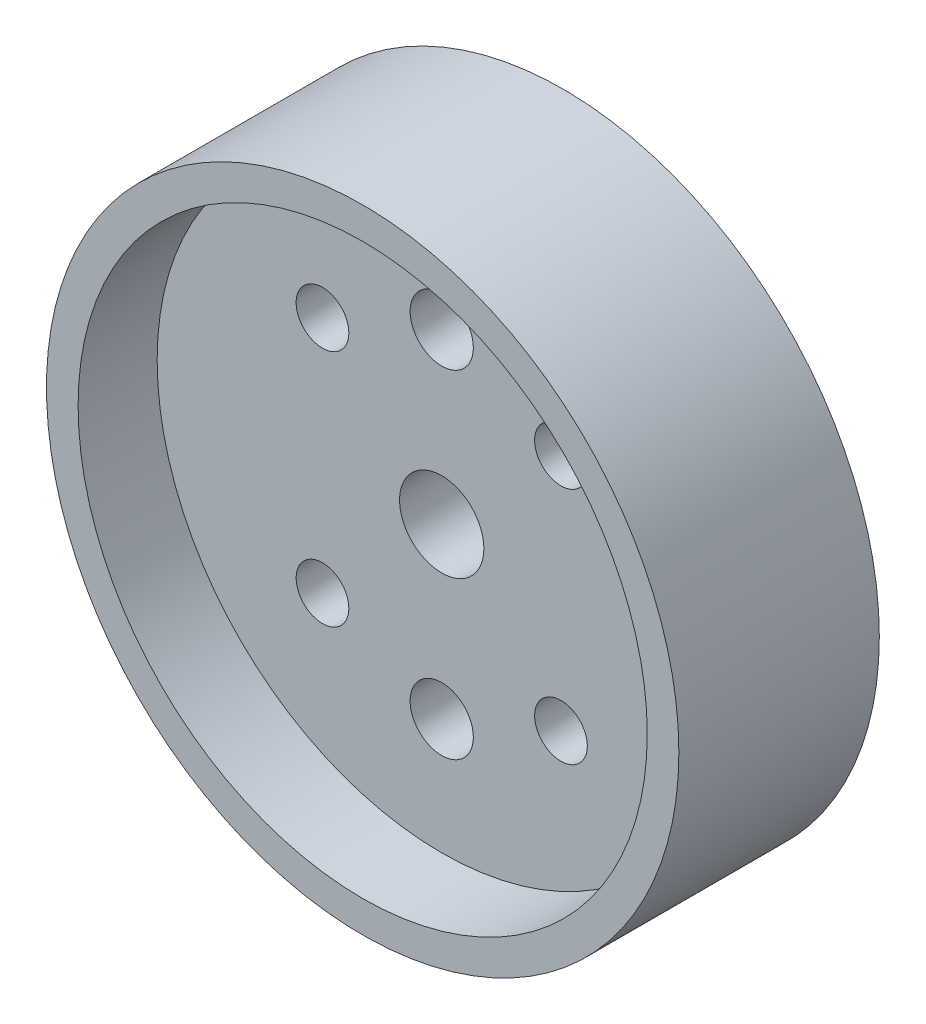
SolidWorks part; units mm, degrees
material "AISI 1020"
ref_plane "Plano frontal" through (0, 0, 0) normal (0, 0, 1) x (1, 0, 0)
ref_plane "Plano superior" through (0, 0, 0) normal (0, 1, 0) x (1, 0, 0)
ref_plane "Plano direito" through (0, 0, 0) normal (1, 0, 0) x (0, 0, -1)
sketch "Esboço1" plane through (0, 0, 0) normal (0, 0, 1) x (1, 0, 0)
  line L5 (-30, -30) -> (30, 30) construction
  line L6 (-30, 30) -> (30, -30) construction
  circle A0 centre (0, 0) radius 30
  point P0 (0, 0)
  dimension "D1" = 60
  dimension "D2" = 60
extrude "Ressalto-extrusão1" add sketch "Esboço1" along normal blind 19.02
sketch "Esboço2" plane through (0, 0, 19.02) normal (0, 0, 1) x (1, 0, 0)
  circle A0 centre (0, 0) radius 26
  dimension "D1" = 52
extrude "Corte-extrusão1" cut sketch "Esboço2" against normal blind 7
sketch "Esboço7" plane through (0, 0, 19.02) normal (0, 0, 1) x (1, 0, 0)
  circle A0 centre (0, 0) radius 27
  dimension "D1" = 54
extrude "Corte-extrusão4" cut sketch "Esboço7" against normal blind 7.5
sketch "Esboço13" plane through (0, 0, 11.52) normal (0, 0, 1) x (1, 0, 0)
  circle A1 centre (0, 16) radius 3
  circle A2 centre (0, -16) radius 3
  circle A3 centre (-11.3137, 11.3137) radius 2.5
  circle A4 centre (11.3137, 11.3137) radius 2.5
  circle A5 centre (-11.3137, -11.3137) radius 2.5
  circle A6 centre (11.3137, -11.3137) radius 2.5
  dimension "D1" = 32
  dimension "D4" = 5
  dimension "D5" = 5
  dimension "D6" = 5
  dimension "D7" = 5
  dimension "D8" = 6
  dimension "D9" = 6
extrude "Corte-extrusão10" cut sketch "Esboço13" against normal through all
sketch "Esboço14" plane through (0, 0, 11.52) normal (0, 0, 1) x (1, 0, 0)
  circle A0 centre (0, 0) radius 4
extrude "Corte-extrusão11" cut sketch "Esboço14" against normal through all
sketch "Esboço16" plane through (0, 0, 0) normal (0, 0, -1) x (-1, 0, 0)
  circle A0 centre (0, 16) radius 5.25
  circle A1 centre (0, -16) radius 5.25
  circle A2 centre (11.3137, 11.3137) radius 4.5
  circle A3 centre (-11.3137, 11.3137) radius 4.5
  circle A4 centre (-11.3137, -11.3137) radius 4.5
  circle A5 centre (11.3137, -11.3137) radius 4.5
extrude "Corte-extrusão12" cut sketch "Esboço16" against normal blind 6
